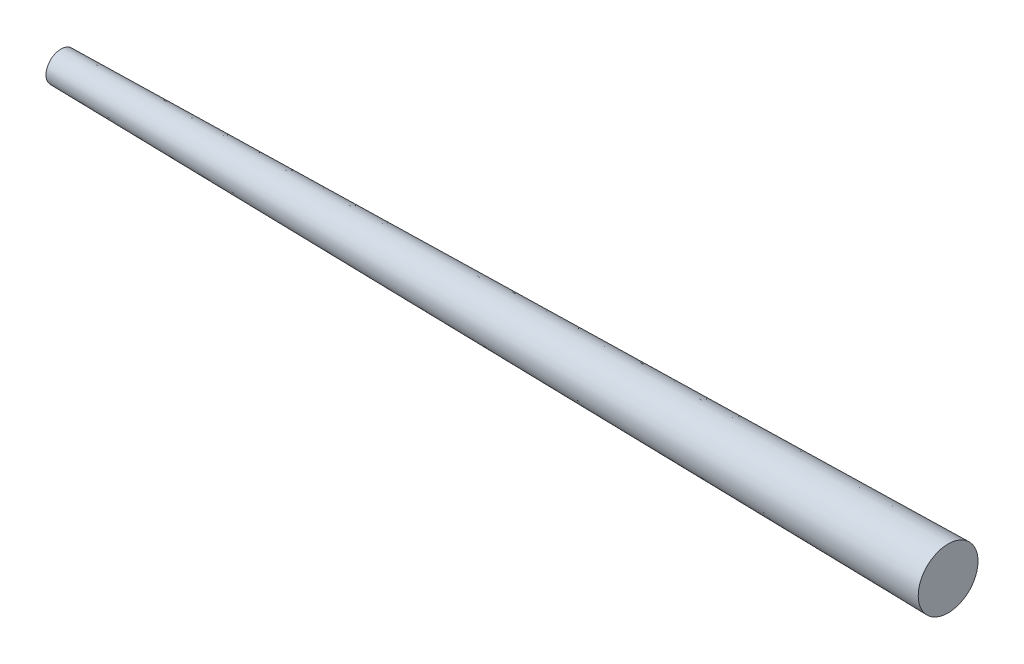
SolidWorks part; units mm, degrees
ref_plane "Ebene vorne" through (0, 0, 0) normal (0, 0, 1) x (1, 0, 0)
ref_plane "Ebene oben" through (0, 0, 0) normal (0, 1, 0) x (1, 0, 0)
ref_plane "Ebene rechts" through (0, 0, 0) normal (1, 0, 0) x (0, 0, -1)
sketch "Skizze1" plane through (0, 0, 0) normal (0, 0, 1) x (1, 0, 0)
  line L0 (-5.5634, 0) -> (-5.5634, 1.5)
  line L1 (-5.5634, 1.5) -> (83.4366, 3)
  line L2 (83.4366, 3) -> (83.4366, 0)
  line L3 (83.4366, 0) -> (-5.5634, 0)
  dimension "D1" = 1.5
  dimension "D2" = 89
  dimension "D3" = 3
revolve "Rotation1" add sketch "Skizze1" angle 360 about L3
